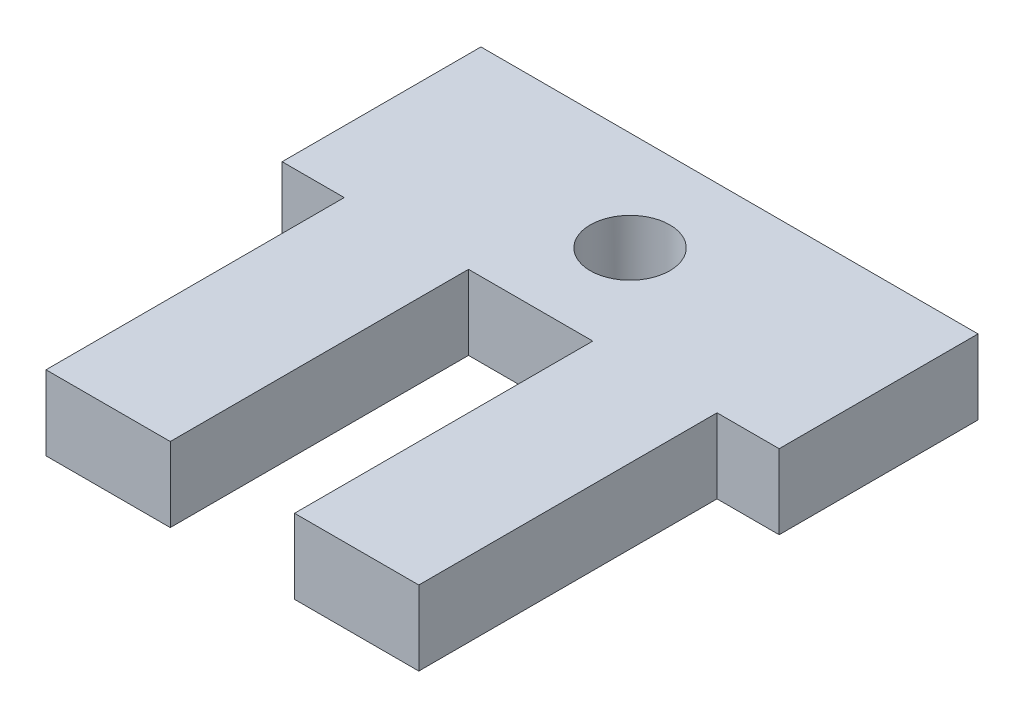
SolidWorks part; units mm, degrees
ref_plane "Front Plane" through (0, 0, 0) normal (0, 0, 1) x (1, 0, 0)
ref_plane "Top Plane" through (0, 0, 0) normal (0, 1, 0) x (1, 0, 0)
ref_plane "Right Plane" through (0, 0, 0) normal (1, 0, 0) x (0, 0, -1)
sketch "Sketch1" plane through (0, 0, 0) normal (0, 1, 0) x (1, 0, 0)
  line L1 (0, 0) -> (20, 0)
  line L2 (0, 0) -> (0, 20)
  line L3 (0, 20) -> (20, 20)
  line L4 (20, 0) -> (20, 20)
  dimension "D1" = 20
  dimension "D2" = 20
extrude "Boss-Extrude1" add sketch "Sketch1" along normal blind 3
sketch "Sketch2" plane through (0, 3, 0) normal (0, 1, 0) x (1, 0, 0)
  line L0 (0, 0) -> (20, 0) construction
  line L1 (0, 12) -> (2.5, 12)
  line L2 (0, 12) -> (0, 0)
  line L3 (0, 0) -> (2.5, 0)
  line L4 (2.5, 12) -> (2.5, 0)
  line L6 (0, 20) -> (0, 0) construction
  dimension "D1" = 12
  dimension "D2" = 2.5
extrude "Cut-Extrude1" cut sketch "Sketch2" against normal up to next (3 mm away)
ref_plane "Plane1" through (10, 0, 0) normal (-1, 0, 0) x (0, 0, 1)
mirror "Mirror1" about plane through (10, 0, 0) normal (-1, 0, 0) of "Cut-Extrude1"
sketch "Sketch3" plane through (0, 3, 0) normal (0, 1, 0) x (1, 0, 0)
  line L0 (10, 1.65) -> (10, -1.65) construction
  line L1 (2.5, 12) -> (0, 12) construction
  circle A0 centre (10, 16) radius 1.6
  dimension "D1" = 3.2
  dimension "D2" = 4
extrude "Cut-Extrude2" cut sketch "Sketch3" against normal through all both and the other way through all
sketch "Sketch4" plane through (0, 3, 0) normal (0, 1, 0) x (1, 0, 0)
  line L0 (2.5, 0) -> (17.5, 0) construction
  line L1 (12.5, 0) -> (7.5, 0)
  line L2 (12.5, 0) -> (12.5, 12)
  line L3 (12.5, 12) -> (7.5, 12)
  line L4 (7.5, 0) -> (7.5, 12)
  line L5 (10, 1.65) -> (10, -1.65) construction
  point P6 (10, 12)
  dimension "D1" = 12
  dimension "D2" = 5
extrude "Cut-Extrude3" cut sketch "Sketch4" against normal through all both and the other way through all
